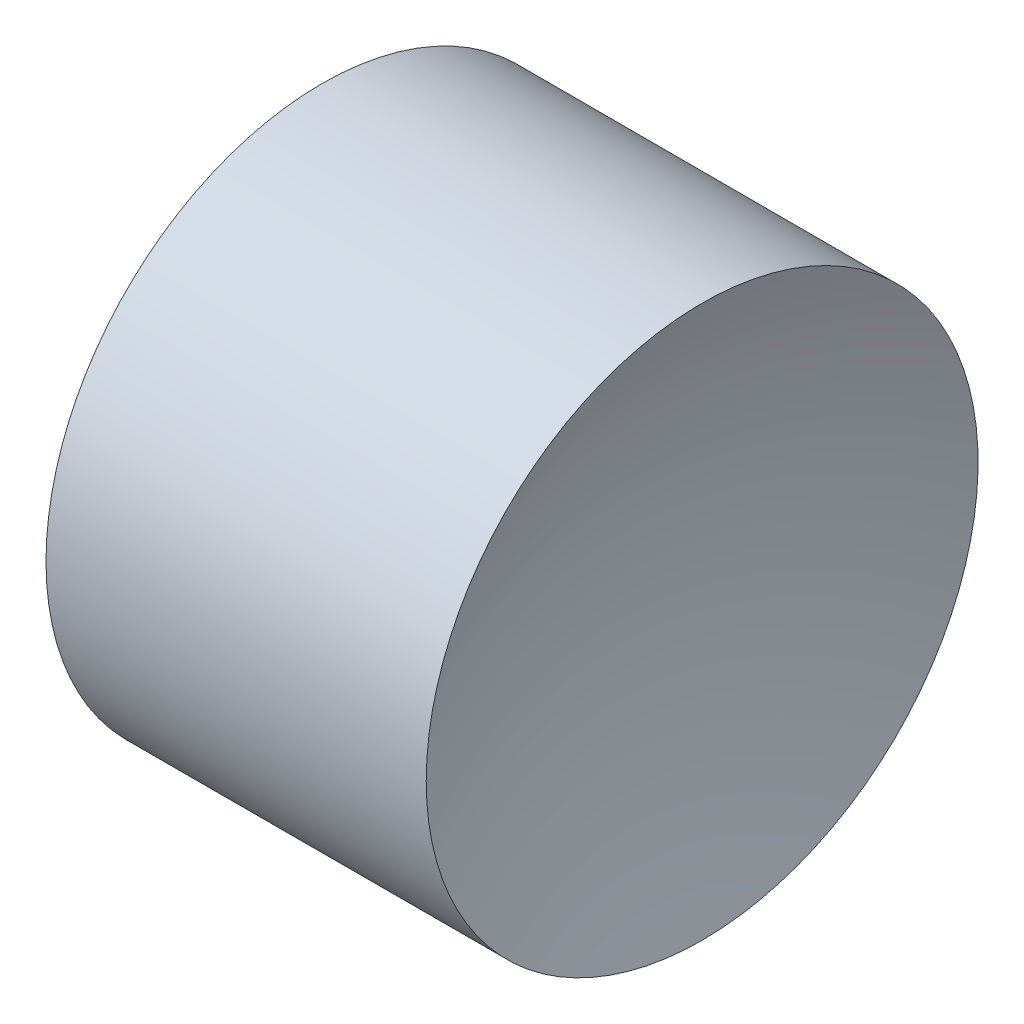
SolidWorks part; units mm, degrees
ref_plane "前视基准面" through (0, 0, 0) normal (0, 0, 1) x (1, 0, 0)
ref_plane "上视基准面" through (0, 0, 0) normal (0, 1, 0) x (1, 0, 0)
ref_plane "右视基准面" through (0, 0, 0) normal (1, 0, 0) x (0, 0, -1)
sketch "草图1" plane through (0, 0, 0) normal (0, 0, 1) x (1, 0, 0)
  line L0 (5.3062, 3.2611) -> (6.9581, 3.2611) construction
  line L1 (5.4896, 3.2611) -> (6.4896, 3.2611)
  line L3 (5.9896, 4.2611) -> (6.6786, 4.2611)
  line L4 (5.9896, 4.2611) -> (5.3006, 4.2611)
  arc A0 (5.4896, 3.2611) -> (5.3006, 4.2611) centre (2.7496, 3.2611) ccw
  arc A1 (6.6786, 4.2611) -> (6.4896, 3.2611) centre (9.2296, 3.2611) ccw
  dimension "D1" = 2.74
  dimension "D2" = 2.74
  dimension "D3" = 1.378
revolve "旋转1" add sketch "草图1" angle 360 about L0
